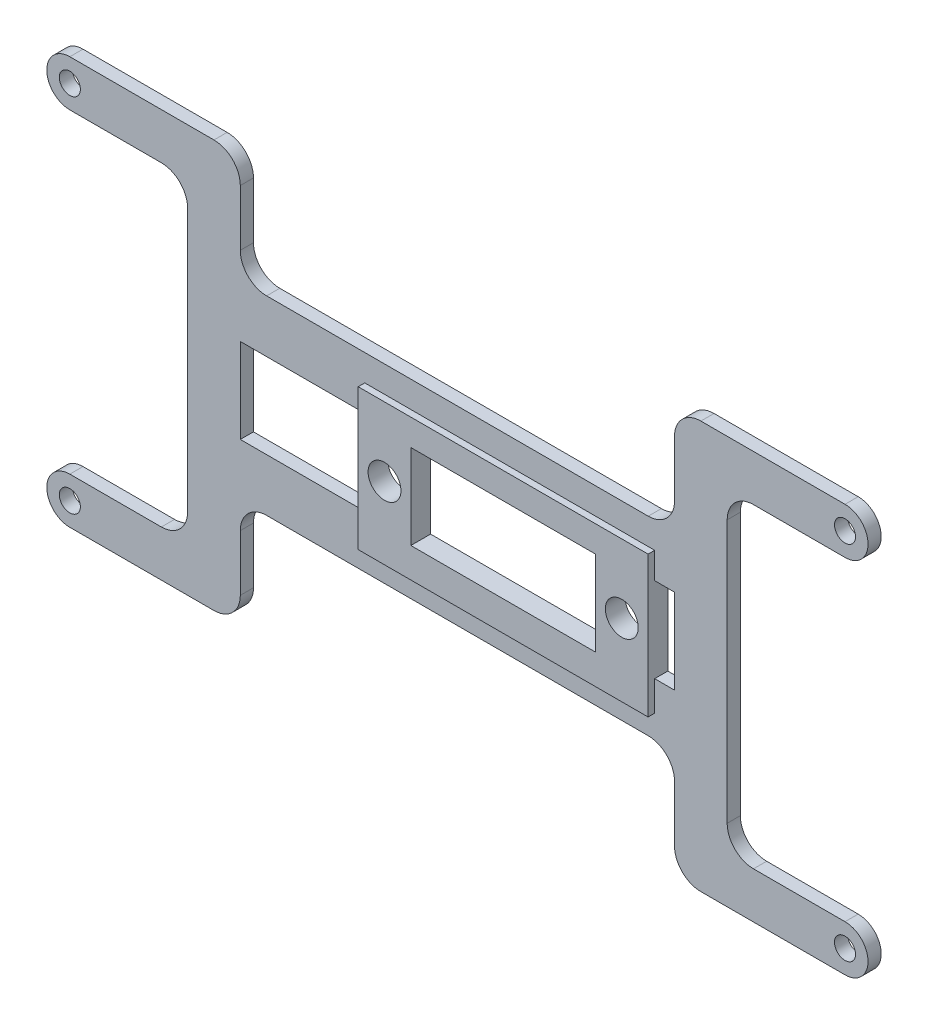
SolidWorks part; units mm, degrees
ref_plane "Front Plane" through (0, 0, 0) normal (0, 0, 1) x (1, 0, 0)
ref_plane "Top Plane" through (0, 0, 0) normal (0, 1, 0) x (1, 0, 0)
ref_plane "Right Plane" through (0, 0, 0) normal (1, 0, 0) x (0, 0, -1)
sketch "Sketch1" plane through (0, 0, 0) normal (0, 0, 1) x (1, 0, 0)
  line L1 (0, 0) -> (0, 3.5)
  line L4 (0, 0) -> (0, 54.9422)
  line L5 (0, 3.5) -> (37.9119, 3.5)
  line L6 (79.9119, 40.9711) -> (79.9119, 13.9711)
  line L7 (0, 51.4422) -> (37.9119, 51.4422)
  line L9 (45.9119, 51.4422) -> (45.9119, 58.4422)
  line L10 (117.8238, 58.4422) -> (71.9119, 58.4422)
  line L11 (66.9119, 5.9711) -> (71.9119, 5.9711)
  line L12 (71.9119, 5.9711) -> (71.9119, 3.5)
  line L13 (117.8238, -3.5) -> (71.9119, -3.5)
  line L15 (66.9119, 40.9711) -> (50.9119, 40.9711)
  line L17 (66.9119, 48.9711) -> (50.9119, 48.9711)
  line L18 (66.9119, 13.9711) -> (50.9119, 13.9711)
  line L19 (66.9119, 5.9711) -> (50.9119, 5.9711)
  line L22 (71.9119, 27.4711) -> (71.9119, 40.9711)
  line L23 (66.9119, 13.9711) -> (71.9119, 13.9711)
  line L24 (79.9119, 13.9711) -> (79.9119, 3.5)
  line L25 (71.9119, 3.5) -> (71.9119, -3.5)
  line L26 (79.9119, 3.5) -> (117.8238, 3.5)
  line L27 (71.9119, 27.4711) -> (71.9119, 13.9711)
  line L28 (50.9119, 5.9711) -> (45.9119, 5.9711)
  line L29 (45.9119, 5.9711) -> (45.9119, 3.5)
  line L30 (50.9119, 13.9711) -> (45.9119, 13.9711)
  line L31 (37.9119, 13.9711) -> (37.9119, 3.5)
  line L32 (79.9119, 40.9711) -> (79.9119, 51.4422)
  line L33 (66.9119, 40.9711) -> (71.9119, 40.9711)
  line L34 (66.9119, 48.9711) -> (71.9119, 48.9711)
  line L35 (71.9119, 48.9711) -> (71.9119, 51.4422)
  line L36 (50.9119, 48.9711) -> (45.9119, 48.9711)
  line L37 (45.9119, 48.9711) -> (45.9119, 51.4422)
  line L38 (37.9119, 40.9711) -> (37.9119, 51.4422)
  line L39 (50.9119, 40.9711) -> (45.9119, 40.9711)
  line L41 (45.9119, 3.5) -> (45.9119, -3.5)
  line L42 (45.9119, -3.5) -> (0, -3.5)
  line L43 (71.9119, 51.4422) -> (71.9119, 58.4422)
  line L44 (45.9119, 58.4422) -> (0, 58.4422)
  line L45 (79.9119, 51.4422) -> (117.8238, 51.4422)
  line L46 (37.9119, 40.9711) -> (37.9119, 13.9711)
  line L48 (45.9119, 27.4711) -> (45.9119, 40.9711)
  line L49 (45.9119, 27.4711) -> (45.9119, 13.9711)
  circle A0 centre (0, 54.9422) radius 1.6
  circle A1 centre (117.8238, 54.9422) radius 1.6
  circle A2 centre (117.8238, 0) radius 1.6
  circle A3 centre (0, 0) radius 1.6
  arc A4 (0, 58.4422) -> (0, 51.4422) centre (0, 54.9422) ccw
  arc A5 (117.8238, 51.4422) -> (117.8238, 58.4422) centre (117.8238, 54.9422) ccw
  arc A6 (117.8238, -3.5) -> (117.8238, 3.5) centre (117.8238, 0) ccw
  arc A7 (0, 3.5) -> (0, -3.5) centre (0, 0) ccw
  circle A8 centre (66.9119, 44.9711) radius 2.1
  circle A9 centre (66.9119, 9.9711) radius 2.1
  circle A14 centre (50.9119, 9.9711) radius 2.1
  circle A15 centre (50.9119, 44.9711) radius 2.1
  point P32 (58.9119, 40.9711)
  point P34 (58.9119, 48.9711)
  point P36 (58.9119, 13.9711)
  point P41 (58.9119, 5.9711)
  dimension "D1" = 54.9422
  dimension "D2" = 3.5
  dimension "D3" = 117.8238
extrude "Boss-Extrude3" add sketch "Sketch1" along normal blind 2
sketch "Sketch3" plane through (0, 0, 2) normal (0, 0, 1) x (1, 0, 0)
  line L0 (71.9119, 13.9711) -> (99.9119, 13.9711)
  line L1 (99.9119, 13.9711) -> (99.9119, 3.5)
  line L2 (79.9119, 3.5) -> (117.8238, 3.5) construction
  line L3 (71.9119, 13.9711) -> (71.9119, 5.9711)
  line L4 (71.9119, 5.9711) -> (91.9119, 5.9711)
  line L5 (91.9119, 5.9711) -> (91.9119, 3.5)
  line L6 (91.9119, 3.5) -> (99.9119, 3.5)
  line L12 (91.9119, 51.4422) -> (99.9119, 51.4422)
  line L13 (91.9119, 48.9711) -> (91.9119, 51.4422)
  line L14 (71.9119, 48.9711) -> (91.9119, 48.9711)
  line L15 (71.9119, 40.9711) -> (71.9119, 48.9711)
  line L16 (99.9119, 40.9711) -> (99.9119, 51.4422)
  line L17 (71.9119, 40.9711) -> (99.9119, 40.9711)
  line L18 (45.9119, 40.9711) -> (17.9119, 40.9711)
  line L19 (17.9119, 40.9711) -> (17.9119, 51.4422)
  line L20 (45.9119, 40.9711) -> (45.9119, 48.9711)
  line L21 (45.9119, 48.9711) -> (25.9119, 48.9711)
  line L22 (25.9119, 48.9711) -> (25.9119, 51.4422)
  line L23 (25.9119, 51.4422) -> (17.9119, 51.4422)
  line L24 (25.9119, 3.5) -> (17.9119, 3.5)
  line L25 (25.9119, 5.9711) -> (25.9119, 3.5)
  line L26 (45.9119, 5.9711) -> (25.9119, 5.9711)
  line L27 (45.9119, 13.9711) -> (45.9119, 5.9711)
  line L28 (17.9119, 13.9711) -> (17.9119, 3.5)
  line L29 (45.9119, 13.9711) -> (17.9119, 13.9711)
extrude "Boss-Extrude4" add sketch "Sketch3" against normal up to surface (2 mm away) up to face at (58.9119, 27.4711, 0)
sketch "Sketch4" plane through (0, 0, 2) normal (0, 0, 1) x (1, 0, 0)
  line L0 (25.9119, 48.9711) -> (25.9119, 65.3112)
  line L1 (25.9119, 48.9711) -> (91.9119, 48.9711)
  line L2 (91.9119, 48.9711) -> (91.9119, 65.3112)
  line L3 (91.9119, 65.3112) -> (25.9119, 65.3112)
  line L4 (25.9119, 5.9711) -> (91.9119, 5.9711)
  line L5 (91.9119, 5.9711) -> (91.9119, -18.7705)
  line L6 (91.9119, -18.7705) -> (25.9119, -18.7705)
  line L7 (25.9119, -18.7705) -> (25.9119, 5.9711)
extrude "Cut-Extrude3" cut sketch "Sketch4" against normal blind 14.5
fillet "Fillet1" radius 4 16 edges at (25.9119, 48.9711, 1) (25.9119, 58.4422, 1) (17.9119, 51.4422, 1) (17.9119, 40.9711, 1) (25.9119, 5.9711, 1) (25.9119, -3.5, 1) (17.9119, 3.5, 1) (17.9119, 13.9711, 1) (99.9119, 13.9711, 1) (99.9119, 3.5, 1) (91.9119, 5.9711, 1) (91.9119, -3.5, 1) (99.9119, 40.9711, 1) (99.9119, 51.4422, 1) (91.9119, 48.9711, 1) (91.9119, 58.4422, 1)
sketch "Sketch5" plane through (0, 0, 2) normal (0, 0, 1) x (1, 0, 0)
  line L0 (45.9119, 40.9711) -> (45.9119, 13.9711)
  line L3 (45.9119, 13.9711) -> (71.9119, 13.9711)
  line L5 (71.9119, 13.9711) -> (71.9119, 40.9711)
  line L6 (71.9119, 40.9711) -> (45.9119, 40.9711)
  circle A0 centre (58.9119, 27.4711) radius 6
extrude "Boss-Extrude5" add sketch "Sketch5" against normal up to surface (2 mm away) up to face at (58.9119, 27.4711, 0)
sketch "Sketch6" plane through (0, 0, 2) normal (0, 0, 1) x (1, 0, 0)
  line L0 (37.9119, 40.9711) -> (42.9119, 40.9711)
  line L1 (37.9119, 13.9711) -> (42.9119, 13.9711)
  line L2 (42.9119, 13.9711) -> (42.9119, 40.9711)
  line L3 (37.9119, 40.9711) -> (37.9119, 13.9711)
  line L4 (79.9119, 13.9711) -> (74.9119, 13.9711)
  line L5 (74.9119, 13.9711) -> (74.9119, 40.9711)
  line L6 (74.9119, 40.9711) -> (79.9119, 40.9711)
  line L7 (79.9119, 40.9711) -> (79.9119, 13.9711)
extrude "Cut-Extrude4" cut sketch "Sketch6" against normal blind 14.5
sketch "Sketch7" plane through (0, 0, 2) normal (0, 0, 1) x (1, 0, 0)
  line L1 (80.8919, 27.4711) -> (80.8919, 40.9711)
  line L2 (74.9119, 40.9711) -> (95.9119, 40.9711) construction
  line L3 (88.8919, 27.4711) -> (88.8919, 40.9711)
  line L4 (80.8919, 27.4711) -> (80.8919, 13.9711)
  line L5 (95.9119, 13.9711) -> (74.9119, 13.9711) construction
  line L6 (80.8919, 13.9711) -> (88.8919, 13.9711)
  line L7 (88.8919, 13.9711) -> (88.8919, 27.4711)
  line L8 (88.8919, 40.9711) -> (80.8919, 40.9711)
  circle A1 centre (84.8919, 27.4711) radius 2.5
extrude "Boss-Extrude6" add sketch "Sketch7" against normal up to surface (2 mm away) up to face at (1.6, 0, 0)
sketch "Sketch8" plane through (0, 0, 2) normal (0, 0, 1) x (1, 0, 0)
  circle A0 centre (48.8309, 27.4711) radius 2.5
extrude "Cut-Extrude5" cut sketch "Sketch8" against normal blind 10
sketch "Sketch9" plane through (0, 0, 2) normal (0, 0, 1) x (1, 0, 0)
  line L1 (42.9119, 40.9711) -> (44.8309, 40.9711)
  line L2 (74.9119, 40.9711) -> (74.9119, 13.9711)
  line L3 (74.9119, 13.9711) -> (52.8309, 13.9711)
  line L4 (42.9119, 13.9711) -> (42.9119, 40.9711)
  line L5 (44.8309, 27.4711) -> (44.8309, 40.9711)
  line L8 (52.8309, 40.9711) -> (52.8309, 13.9711)
  line L10 (44.8309, 27.4711) -> (44.8309, 13.9711)
  line L11 (52.8309, 40.9711) -> (74.9119, 40.9711)
  line L12 (44.8309, 13.9711) -> (42.9119, 13.9711)
extrude "Cut-Extrude6" cut sketch "Sketch9" against normal blind 10
sketch "Sketch10" plane through (0, 0, 2) normal (0, 0, 1) x (1, 0, 0)
  line L2 (44.8309, 13.9711) -> (44.8309, 40.9711) construction
  line L5 (44.8309, 13.9711) -> (44.8309, 13.0211)
  line L6 (44.8309, 13.0211) -> (88.8919, 13.0211)
  line L7 (88.8919, 13.9711) -> (88.8919, 40.9711) construction
  line L8 (88.8919, 13.0211) -> (88.8919, 13.9711)
  line L9 (88.8919, 40.9711) -> (88.8919, 41.9211)
  line L10 (88.8919, 41.9211) -> (44.8309, 41.9211)
  line L11 (44.8309, 41.9211) -> (44.8309, 40.9711)
  line L12 (44.8309, 40.9711) -> (12.9645, 40.9711)
  line L13 (12.9645, 40.9711) -> (12.9645, 51.4422)
  line L14 (0, 51.4422) -> (13.9119, 51.4422) construction
  line L15 (12.9645, 51.4422) -> (106.0206, 51.4422)
  line L16 (103.9119, 51.4422) -> (117.8238, 51.4422) construction
  line L17 (106.0206, 51.4422) -> (106.0206, 40.9711)
  line L18 (106.0206, 40.9711) -> (88.8919, 40.9711)
  line L19 (44.8309, 13.9711) -> (12.9645, 13.9711)
  line L20 (12.9645, 13.9711) -> (12.9645, 3.5)
  line L22 (106.0206, 3.5) -> (106.0206, 13.9711)
  line L23 (106.0206, 13.9711) -> (88.8919, 13.9711)
  line L26 (12.9645, 3.5) -> (106.0206, 3.5)
extrude "Cut-Extrude7" cut sketch "Sketch10" against normal blind 10
sketch "Sketch11" plane through (0, 0, 2) normal (0, 0, 1) x (1, 0, 0)
  line L1 (52.8309, 33.9211) -> (80.8919, 33.9211)
  line L2 (80.8919, 40.9711) -> (80.8919, 13.9711) construction
  line L3 (80.8919, 33.9211) -> (80.8919, 40.9711)
  line L4 (80.8919, 40.9711) -> (52.8309, 40.9711)
  line L5 (52.8309, 40.9711) -> (52.8309, 33.9211)
  line L6 (52.8309, 40.9711) -> (52.8309, 13.9711) construction
  line L8 (52.8309, 21.0211) -> (80.8919, 21.0211)
  line L9 (80.8919, 21.0211) -> (80.8919, 13.9711)
  line L10 (80.8919, 13.9711) -> (52.8309, 13.9711)
  line L11 (52.8309, 13.9711) -> (52.8309, 21.0211)
extrude "Boss-Extrude7" add sketch "Sketch11" against normal up to surface (2 mm away) up to face at (66.8614, 27.4711, 0)
sketch "Sketch12" plane through (0, 0, 2) normal (0, 0, 1) x (1, 0, 0)
  line L0 (25.9119, 1.2355) -> (25.9119, 54.4422)
  line L1 (25.9119, 0.5) -> (25.9119, 1.9711) construction
  line L2 (25.9119, 54.4422) -> (91.9119, 54.4422)
  line L3 (91.9119, 54.4422) -> (91.9119, 0.5)
  line L4 (91.9119, 0.5) -> (25.9119, 1.2355)
  line L5 (44.8309, 41.9211) -> (44.8309, 13.0211)
  line L6 (44.8309, 13.0211) -> (88.8919, 13.0211)
  line L7 (88.8919, 13.0211) -> (88.8919, 41.9211)
  line L8 (88.8919, 41.9211) -> (44.8309, 41.9211)
extrude "Cut-Extrude9" cut sketch "Sketch12" against normal blind 10
sketch "Sketch13" plane through (0, 0, 2) normal (0, 0, 1) x (1, 0, 0)
  line L0 (25.9119, 3.5) -> (25.9119, 13.0211)
  line L1 (44.8309, 13.0211) -> (25.9119, 13.0211)
  line L2 (25.9119, 41.9211) -> (25.9119, 51.4422)
  line L3 (17.9119, 13.0211) -> (17.9119, 3.5)
  line L4 (0, 3.5) -> (25.9119, 3.5) construction
  line L5 (17.9119, 13.0211) -> (17.9119, 51.4422)
  line L6 (0, 51.4422) -> (25.9119, 51.4422) construction
  line L7 (91.9119, 51.4422) -> (91.9119, 41.9211)
  line L8 (88.8919, 41.9211) -> (91.9119, 41.9211)
  line L9 (91.9119, 33.9211) -> (88.8919, 33.9211)
  line L10 (99.9119, 41.9211) -> (99.9119, 51.4422)
  line L11 (91.9119, 51.4422) -> (117.8238, 51.4422) construction
  line L12 (99.9119, 51.4422) -> (99.9119, 3.5)
  line L13 (91.9119, 3.5) -> (117.8238, 3.5) construction
  line L14 (88.8919, 13.0211) -> (88.8919, 41.9211) construction
  line L15 (88.8919, 13.0211) -> (91.9119, 13.0211)
  line L16 (88.8919, 33.9211) -> (88.8919, 41.9211)
  line L17 (91.9119, 21.0211) -> (88.8919, 21.0211)
  line L18 (44.8309, 41.9211) -> (25.9119, 41.9211)
  line L19 (91.9119, 33.9211) -> (91.9119, 21.0211)
  line L20 (44.8309, 33.9211) -> (25.9119, 33.9211)
  line L21 (91.9119, 13.0211) -> (91.9119, 3.5)
  line L22 (44.8309, 21.0211) -> (25.9119, 21.0211)
  line L23 (88.8919, 21.0211) -> (88.8919, 13.0211)
  line L24 (44.8309, 13.0211) -> (44.8309, 21.0211)
  line L25 (44.8309, 33.9211) -> (44.8309, 41.9211)
  line L26 (17.9119, 51.4422) -> (25.9119, 51.4422)
  line L27 (25.9119, 3.5) -> (17.9119, 3.5)
  line L28 (91.9119, 3.5) -> (99.9119, 3.5)
  line L29 (91.9119, 51.4422) -> (99.9119, 51.4422)
  line L30 (25.9119, 21.0211) -> (25.9119, 33.9211)
  line M3 (25.9119, 3.5) -> (0, 3.5)
extrude "Boss-Extrude9" add sketch "Sketch13" against normal blind 2 contours L22 L30 L20 L25 L18 L2 L26 L5 L3 L0 L1 L24 M3 | L29 L7 L8 L16 L9 L19 L17 L23 L15 L21 L28 L12 L10
fillet "Fillet2" radius 4 8 edges at (17.9119, 3.5, 1) (17.9119, 51.4422, 1) (25.9119, 41.9211, 1) (25.9119, 13.0211, 1) (91.9119, 13.0211, 1) (91.9119, 41.9211, 1) (99.9119, 3.5, 1) (99.9119, 51.4422, 1)
sketch "Sketch14" plane through (0, 0, 2) normal (0, 0, 1) x (1, 0, 0)
  line L0 (44.8309, 33.9211) -> (44.8309, 37.9211)
  line L2 (88.8919, 33.9211) -> (88.8919, 37.9211)
  line L3 (88.8919, 37.9211) -> (44.8309, 37.9211)
  line L4 (44.8309, 33.9211) -> (44.8309, 21.0211)
  line L5 (44.8309, 21.0211) -> (44.8309, 16.4792)
  line L6 (44.8309, 16.4792) -> (88.8919, 16.4792)
  line L7 (88.8919, 16.4792) -> (88.8919, 21.0211)
  line L8 (88.8919, 21.0211) -> (88.8919, 33.9211)
  line L9 (80.8919, 21.0211) -> (80.8919, 33.9211)
  line L10 (80.8919, 33.9211) -> (52.8309, 33.9211)
  line L11 (52.8309, 33.9211) -> (52.8309, 21.0211)
  line L12 (52.8309, 21.0211) -> (80.8919, 21.0211)
  circle A0 centre (48.8309, 27.4711) radius 2.5
  circle A1 centre (84.8919, 27.4711) radius 2.5
extrude "Boss-Extrude10" add sketch "Sketch14" along normal blind 1
